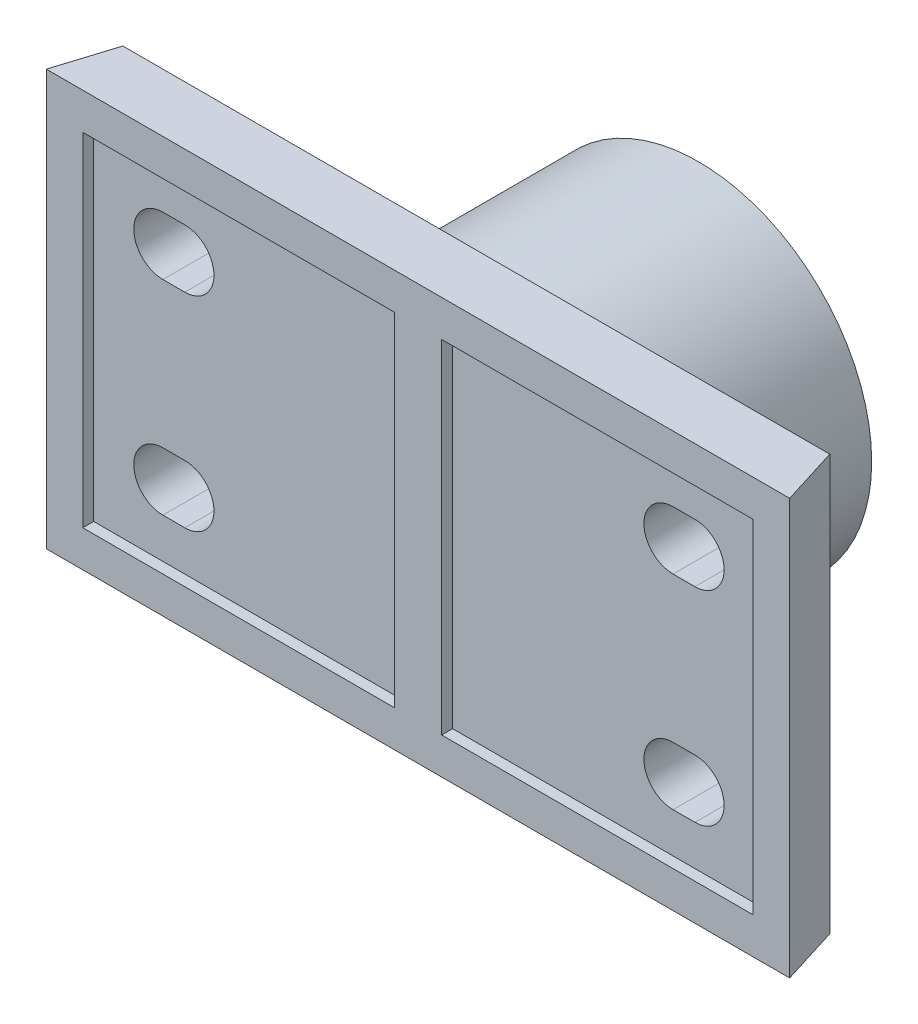
SolidWorks part; units mm, degrees
ref_plane "Front Plane" through (0, 0, 0) normal (0, 0, 1) x (1, 0, 0)
ref_plane "Top Plane" through (0, 0, 0) normal (0, 1, 0) x (1, 0, 0)
ref_plane "Right Plane" through (0, 0, 0) normal (1, 0, 0) x (0, 0, -1)
sketch "Sketch1" plane through (0, 0, 0) normal (0, 1, 0) x (1, 0, 0)
  line L0 (-102, 0) -> (-97, 16)
  line L1 (-97, 16) -> (97, 16)
  line L2 (0, 0) -> (0, 86.6968) construction
  line L4 (0, 0) -> (-102, 0)
  line L11 (0, 0) -> (102, 0)
  line L12 (102, 0) -> (97, 16)
  point P15 (0, 16)
  dimension "D1" = 204
  dimension "D4" = 16
extrude "Boss-Extrude1" add sketch "Sketch1" along normal mid plane 114
sketch "Sketch3" plane through (0, 0, -16) normal (0, 0, -1) x (-1, 0, 0)
  circle A0 centre (0, 0) radius 47.5
  circle A1 centre (0, 0) radius 31
  dimension "D1" = 95
  dimension "D2" = 62
extrude "Boss-Extrude3" add sketch "Sketch3" along normal blind 13
sketch "Sketch4" plane through (0, 0, -29) normal (0, 0, -1) x (-1, 0, 0)
  circle A0 centre (0, 0) radius 47.5
  circle A1 centre (0, 0) radius 32.5
  dimension "D1" = 95
  dimension "D2" = 65
extrude "Boss-Extrude4" add sketch "Sketch4" along normal blind 37
sketch "Sketch5" plane through (0, 0, -66) normal (0, 0, -1) x (-1, 0, 0)
  circle A0 centre (0, 0) radius 47.5
  circle A1 centre (0, 0) radius 31
  dimension "D1" = 62
  dimension "D2" = 95
extrude "Boss-Extrude5" add sketch "Sketch5" along normal blind 11
sketch "Sketch6" plane through (0, 0, -16) normal (0, 0, -1) x (-1, 0, 0)
  line L0 (-73, 28) -> (-67, 28) construction
  line L1 (-73, 36) -> (-67, 36)
  line L2 (-73, 20) -> (-67, 20)
  arc A0 (-73, 36) -> (-73, 20) centre (-73, 28) ccw
  arc A1 (-67, 20) -> (-67, 36) centre (-67, 28) ccw
  point P2 (-70, 28)
  dimension "D1" = 22
  dimension "D2" = 8
  dimension "D3" = 70
  dimension "D4" = 28
sketch "Sketch7" plane through (0, 0, -16) normal (0, 0, -1) x (-1, 0, 0)
  line L0 (-73, -28) -> (-67, -28) construction
  line L1 (-73, -20) -> (-67, -20)
  line L2 (-73, -36) -> (-67, -36)
  arc A0 (-73, -20) -> (-73, -36) centre (-73, -28) ccw
  arc A1 (-67, -36) -> (-67, -20) centre (-67, -28) ccw
  point P2 (-70, -28)
  dimension "D1" = 22
  dimension "D2" = 8
  dimension "D3" = 70
  dimension "D4" = 28
sketch "Sketch8" plane through (0, 0, -16) normal (0, 0, -1) x (-1, 0, 0)
  circle A0 centre (-70, 28) radius 19
  circle A1 centre (-70, -28) radius 19
  dimension "D1" = 38
  dimension "D2" = 38
extrude "Boss-Extrude6" add sketch "Sketch8" along normal blind 3
sketch "Sketch9" plane through (0, 0, 0) normal (0, 0, 1) x (1, 0, 0)
  line L0 (6.5, 47) -> (92, 47)
  line L1 (92, 47) -> (92, -47)
  line L2 (92, -47) -> (6.5, -47)
  line L3 (6.5, -47) -> (6.5, 47)
  line L4 (-102, 57) -> (102, 57) construction
  line L5 (-102, -57) -> (102, -57) construction
  line L6 (102, 57) -> (102, -57) construction
  dimension "D1" = 10
  dimension "D2" = 10
  dimension "D3" = 10
  dimension "D4" = 6.5
extrude "Cut-Extrude1" cut sketch "Sketch9" against normal blind 3
extrude "Cut-Extrude3" cut sketch "Sketch6" against normal mid plane 59 contours A1 L1 A0 L2
extrude "Cut-Extrude4" cut sketch "Sketch7" against normal mid plane 72 contours A1 L1 A0 L2
mirror "Mirror1" about plane through (0, 0, 0) normal (1, 0, 0) of "Cut-Extrude1", "Cut-Extrude3", "Boss-Extrude6", "Cut-Extrude4"
